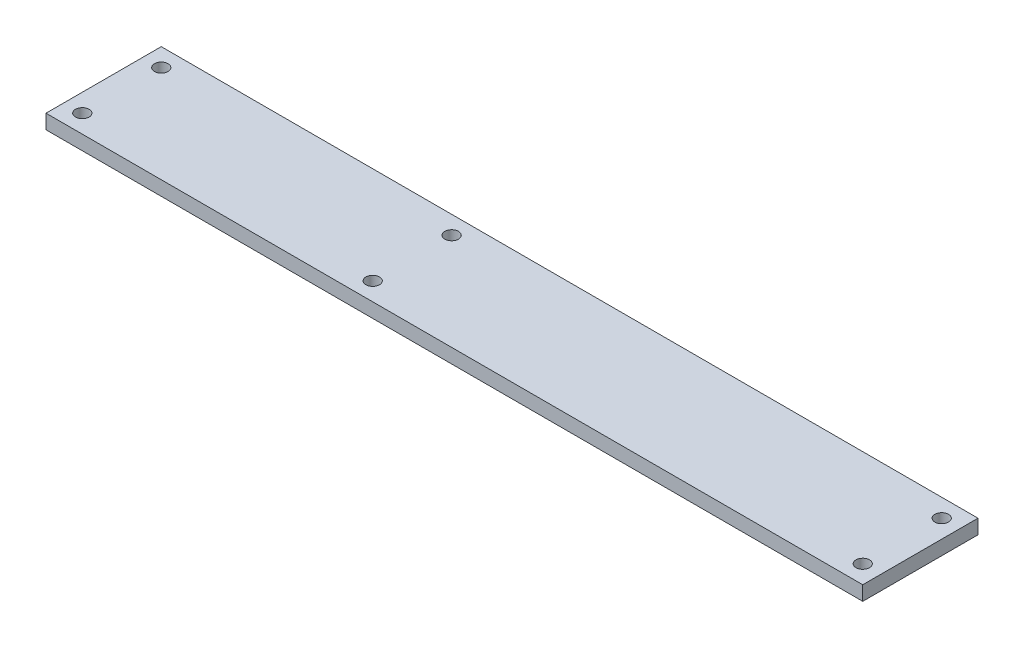
SolidWorks part; units mm, degrees
ref_plane "Alzado" through (0, 0, 0) normal (0, 0, 1) x (1, 0, 0)
ref_plane "Planta" through (0, 0, 0) normal (0, 1, 0) x (1, 0, 0)
ref_plane "Vista lateral" through (0, 0, 0) normal (1, 0, 0) x (0, 0, -1)
sketch "Croquis1" plane through (0, 0, 0) normal (0, 1, 0) x (1, 0, 0)
  line L0 (-22, 8.7) -> (-22, -8.7) construction
  line L1 (-90, -12.7) -> (90, -12.7)
  line L2 (-90, -12.7) -> (-90, 12.7)
  line L3 (-90, 12.7) -> (90, 12.7)
  line L4 (90, -12.7) -> (90, 12.7)
  line L5 (-90, -12.7) -> (90, 12.7) construction
  line L6 (-90, 12.7) -> (90, -12.7) construction
  line L7 (86, -8.7) -> (-86, -8.7) construction
  line L8 (86, -8.7) -> (86, 8.7) construction
  line L9 (86, 8.7) -> (-86, 8.7) construction
  line L10 (-86, -8.7) -> (-86, 8.7) construction
  line L11 (86, -8.7) -> (-86, 8.7) construction
  line L12 (86, 8.7) -> (-86, -8.7) construction
  circle A0 centre (-86, 8.7) radius 1.5
  circle A1 centre (-86, -8.7) radius 1.5
  circle A2 centre (86, -8.7) radius 1.5
  circle A3 centre (86, 8.7) radius 1.5
  circle A4 centre (-22, 8.7) radius 1.5
  circle A5 centre (-22, -8.7) radius 1.5
  point P0 (0, 0)
  point P6 (0, 0)
  dimension "D5" = 3
  dimension "D1" = 25.4
  dimension "D2" = 180
  dimension "D3" = 4
  dimension "D4" = 4
  dimension "D6" = 64
  dimension "D7" = 17.4
extrude "Saliente-Extruir1" add sketch "Croquis1" along normal blind 3.175
